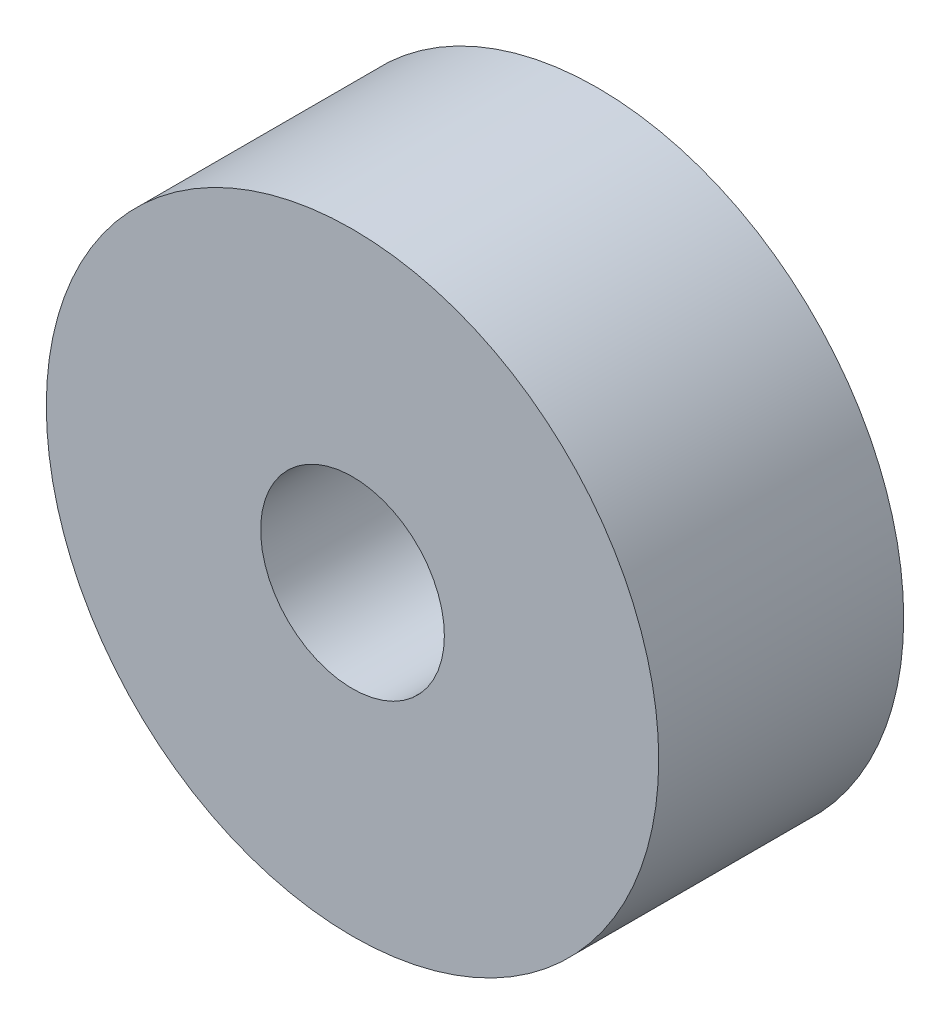
SolidWorks part; units mm, degrees
ref_plane "Plano frontal" through (0, 0, 0) normal (0, 0, 1) x (1, 0, 0)
ref_plane "Plano superior" through (0, 0, 0) normal (0, 1, 0) x (1, 0, 0)
ref_plane "Plano direito" through (0, 0, 0) normal (1, 0, 0) x (0, 0, -1)
sketch "Esboço1" plane through (0, 0, 0) normal (0, 0, 1) x (1, 0, 0)
  circle A0 centre (0, 0) radius 1.5
  circle A1 centre (0, 0) radius 5
  dimension "D1" = 10
  dimension "D2" = 3
extrude "Ressalto-extrusão1" add sketch "Esboço1" along normal blind 4
